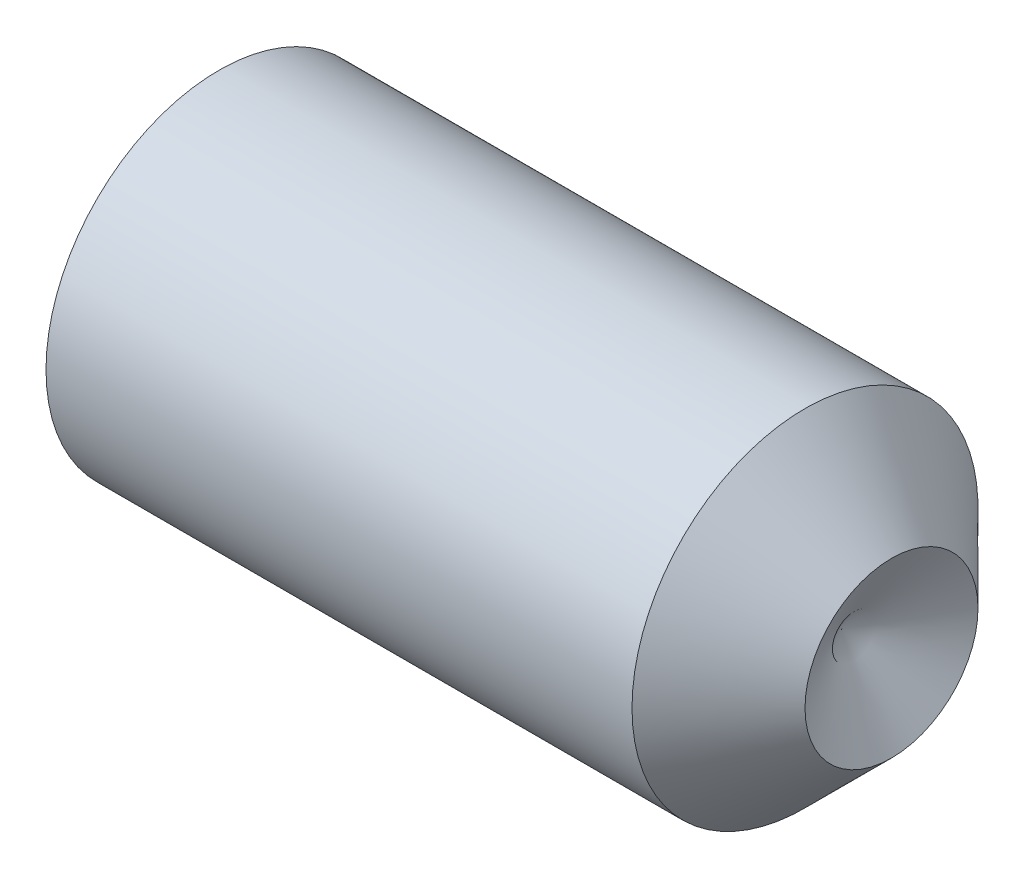
SolidWorks part; units mm, degrees
revolve "BaseBody" add sketch "BodySke" angle 360 about L5
sketch "BodySke" plane through (0, 0, 0) normal (0, 0, 1) x (1, 0, 0)
  line L0 (0, 0) -> (0, 1.61)
  line L1 (0, 1.61) -> (0.2252, 2)
  line L2 (0.2252, 2) -> (7, 2)
  line L3 (7, 2) -> (8, 1)
  line L4 (7.4226, 0) -> (0, 0)
  line L5 (-12.7, 0) -> (88.9, 0) construction
  line L6 (7.4226, 0) -> (8, 1)
  line L7 (8, 1) -> (8, 10.525) construction
  line L8 (0, -1.61) -> (0.2252, -2) construction
  line L9 (7.4226, 0) -> (8, -1) construction
  line L10 (7, -2) -> (8, -1) construction
  line L11 (0.35, 15.875) -> (0.35, -3.175) construction
  dimension "Diameter" = 4
  dimension "Drive_ch_ang" = 60
  dimension "Minor_dia" = 3.22
  dimension "Cup_ang" = 120
  dimension "Cup_dia" = 2
  dimension "Length" = 8
  dimension "Cup_nose_ang" = 45
  dimension "Advance" = 0.7
cosmetic thread "ThreadCosmetic" parameters "Thread_minor"=3.22
ref_plane "Plane1" through (0, 0, 0) normal (0, 0, 1) x (1, 0, 0)
ref_plane "Plane2" through (0, 0, 0) normal (0, 1, 0) x (1, 0, 0)
ref_plane "Plane3" through (0, 0, 0) normal (1, 0, 0) x (0, 0, -1)
sketch "Sketch2" plane through (0, 0, 0) normal (-1, 0, 0) x (0, 0, 1)
  line L0 (0.5774, 1) -> (-0.5774, 1)
  line L1 (-0.5774, 1) -> (-1.1547, 0)
  line L2 (0.5774, 1) -> (1.1547, 0)
  line L3 (0.5774, -1) -> (1.1547, 0)
  line L4 (0.5774, -1) -> (-0.5774, -1)
  line L5 (-0.5774, -1) -> (-1.1547, 0)
  dimension "Hex_size" = 2
  dimension "D2" = 1
  dimension "D3" = 1
extrude "Hex" cut sketch "Sketch2" against normal blind 2.5
sketch "ThdSchSke" plane through (0, 0, 0) normal (0, 0, 1) x (1, 0, 0)
  line L0 (0.2252, -1.61) -> (-0.0479, -2)
  line L1 (0.2252, -1.61) -> (0.4982, -2)
  line L2 (0.4982, -2) -> (0.4982, -2.5)
  line L3 (-3.175, 0) -> (5.1513, 0) construction
  line L4 (0.2252, 2) -> (0.2252, -2) construction
  line L5 (0.4982, -2.5) -> (-0.0479, -2.5)
  line L6 (-0.0479, -2.5) -> (-0.0479, -2)
  dimension "Thread_minor" = 3.22
  dimension "Diameter" = 4
revolve "ThreadSchematic" [suppressed] cut sketch "ThdSchSke" angle 360 about L3
pattern_linear "ThdSchPat" [suppressed]
equation "\"D2@Sketch2\" = \"Hex_size@Sketch2\" / 2"
equation "\"D3@Sketch2\" = \"Hex_size@Sketch2\" / 2"
equation "\"Thread_minor@ThreadCosmetic\" = \"Minor_dia@BodySke\""
equation "\"Thread_minor@ThdSchSke\" = \"Thread_minor@ThreadCosmetic\""
equation "\"Diameter@ThdSchSke\" = \"Diameter@BodySke\""
equation "\"Overcut@ThdSchSke\" = \"Diameter@BodySke\" * 1.25"
equation "\"Num_threads@ThdSchPat\" = int( (\"Length@BodySke\" - ( ( ( \"Diameter@BodySke\" - \"Minor_dia@BodySke\" ) * 0.5 ) / tan( \"Drive_ch_ang@BodySke\" * 0.017453292 ) ) - ( ( ( \"Diameter@BodySke\" - \"Cup_dia@BodySke\" ) * 0.5 ) * tan( \"Cup_nose_ang@BodySke\" * 0.017453292 ) ) ) / \"Advance@BodySke\" + 0.999 )  + 1"
equation "\"Advance@ThdSchPat\" = (\"Length@BodySke\" - ( ( ( \"Diameter@BodySke\" - \"Minor_dia@BodySke\" ) * 0.5 ) / tan( \"Drive_ch_ang@BodySke\" * 0.017453292 ) ) - ( ( ( \"Diameter@BodySke\" - \"Cup_dia@BodySke\" ) * 0.5 ) * tan( \"Cup_nose_ang@BodySke\" * 0.017453292 ) ) ) /  (\"Num_threads@ThdSchPat\" - 1) 'relax it"
equation "' \"Num_threads@ThdSchPat\" = \"Num_threads@ThdSchPat\" - sgn( \"Num_threads@ThdSchPat\" - 1) '---chamfered tips only---"
